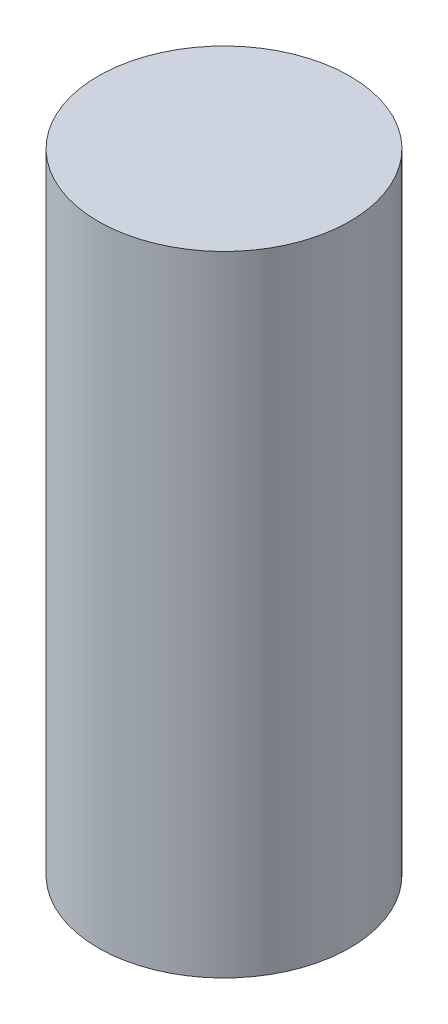
SolidWorks part; units mm, degrees
ref_plane "Front Plane" through (0, 0, 0) normal (0, 0, 1) x (1, 0, 0)
ref_plane "Top Plane" through (0, 0, 0) normal (0, 1, 0) x (1, 0, 0)
ref_plane "Right Plane" through (0, 0, 0) normal (1, 0, 0) x (0, 0, -1)
sketch "Sketch1" plane through (0, 0, 0) normal (0, 1, 0) x (1, 0, 0)
  circle A0 centre (0, 0) radius 5
extrude "Boss-Extrude1" add sketch "Sketch1" along normal blind 25
